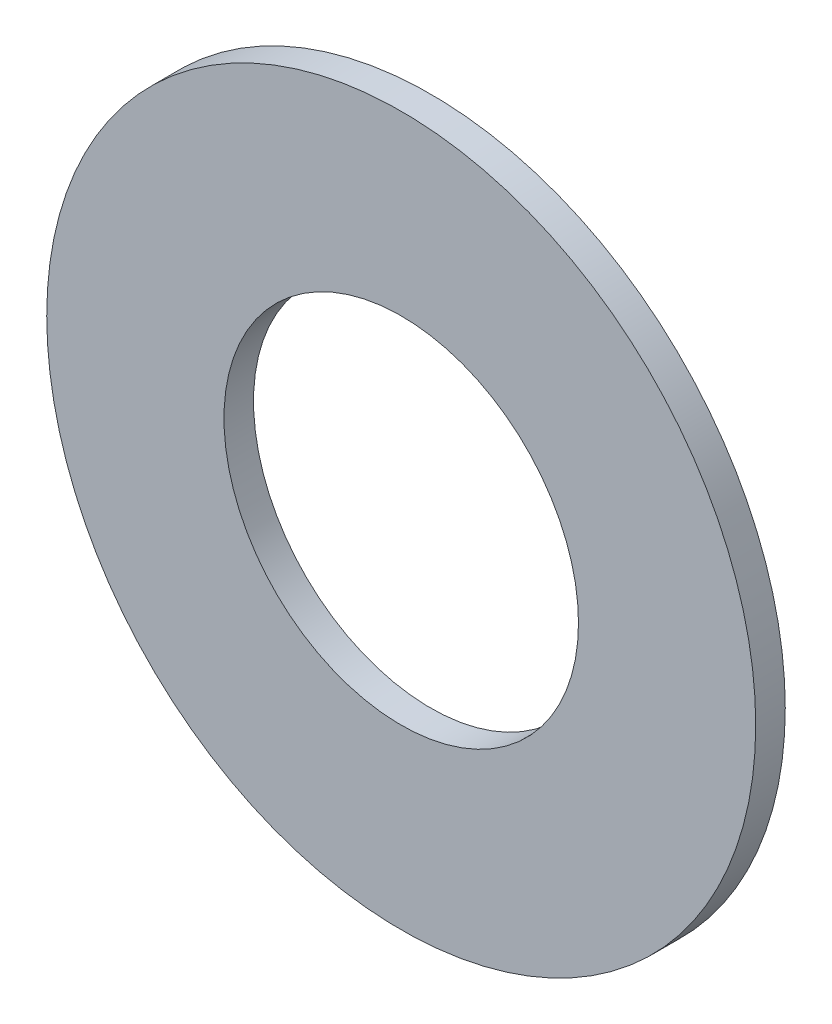
SolidWorks part; units mm, degrees
ref_plane "Front Plane" through (0, 0, 0) normal (0, 0, 1) x (1, 0, 0)
ref_plane "Top Plane" through (0, 0, 0) normal (0, 1, 0) x (1, 0, 0)
ref_plane "Right Plane" through (0, 0, 0) normal (1, 0, 0) x (0, 0, -1)
sketch "Sketch1" plane through (0, 0, 0) normal (0, 0, 1) x (1, 0, 0)
  circle A0 centre (0, 0) radius 4.7625
  circle A1 centre (0, 0) radius 9.525
  dimension "D1" = 9.525
  dimension "D2" = 19.05
extrude "Boss-Extrude1" add sketch "Sketch1" along normal blind 0.7937
